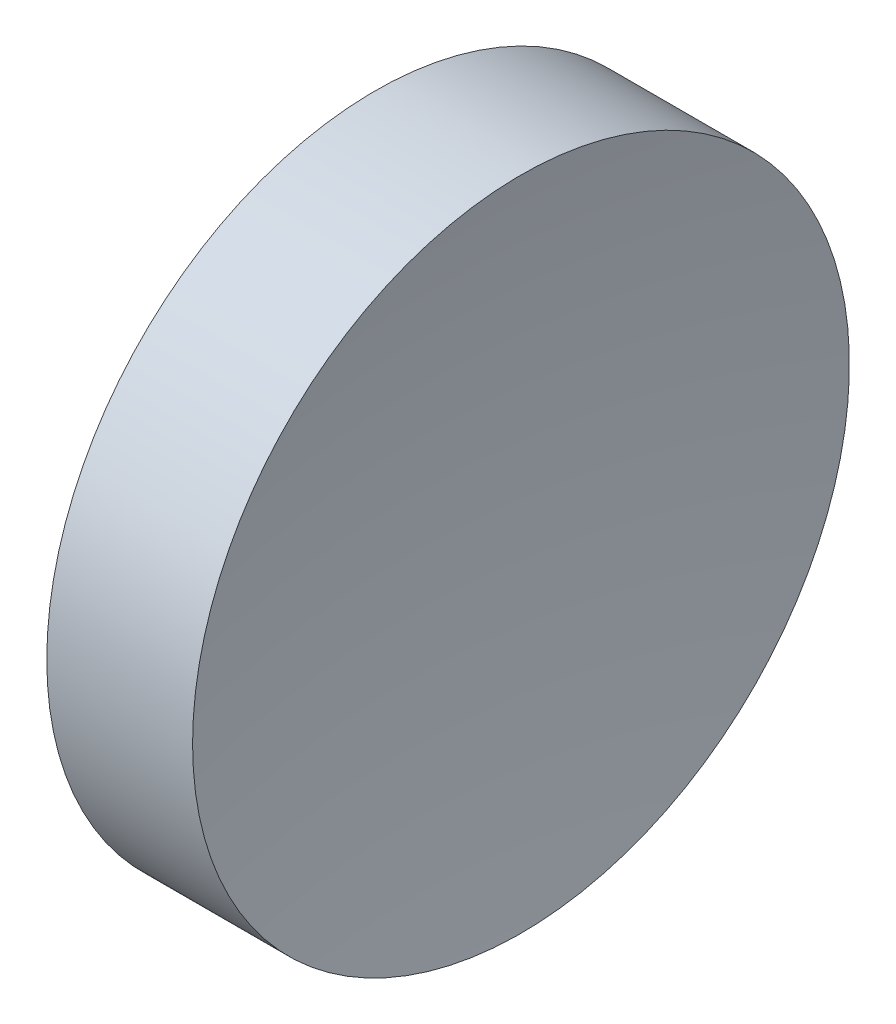
SolidWorks part; units mm, degrees
ref_plane "前视基准面" through (0, 0, 0) normal (0, 0, 1) x (1, 0, 0)
ref_plane "上视基准面" through (0, 0, 0) normal (0, 1, 0) x (1, 0, 0)
ref_plane "右视基准面" through (0, 0, 0) normal (1, 0, 0) x (0, 0, -1)
sketch "草图1" plane through (0, 0, 0) normal (0, 0, 1) x (1, 0, 0)
  line L0 (217.9703, 138.756) -> (265.5527, 138.756) construction
  line L1 (230.1853, 138.756) -> (230.1853, 163.756)
  line L2 (239.1853, 138.756) -> (230.1853, 138.756)
  line L3 (230.1853, 163.756) -> (241.2833, 163.756)
  arc A0 (241.2833, 163.756) -> (239.1853, 138.756) centre (389.1853, 138.756) ccw
revolve "旋转1" add sketch "草图1" angle 360 about L0
